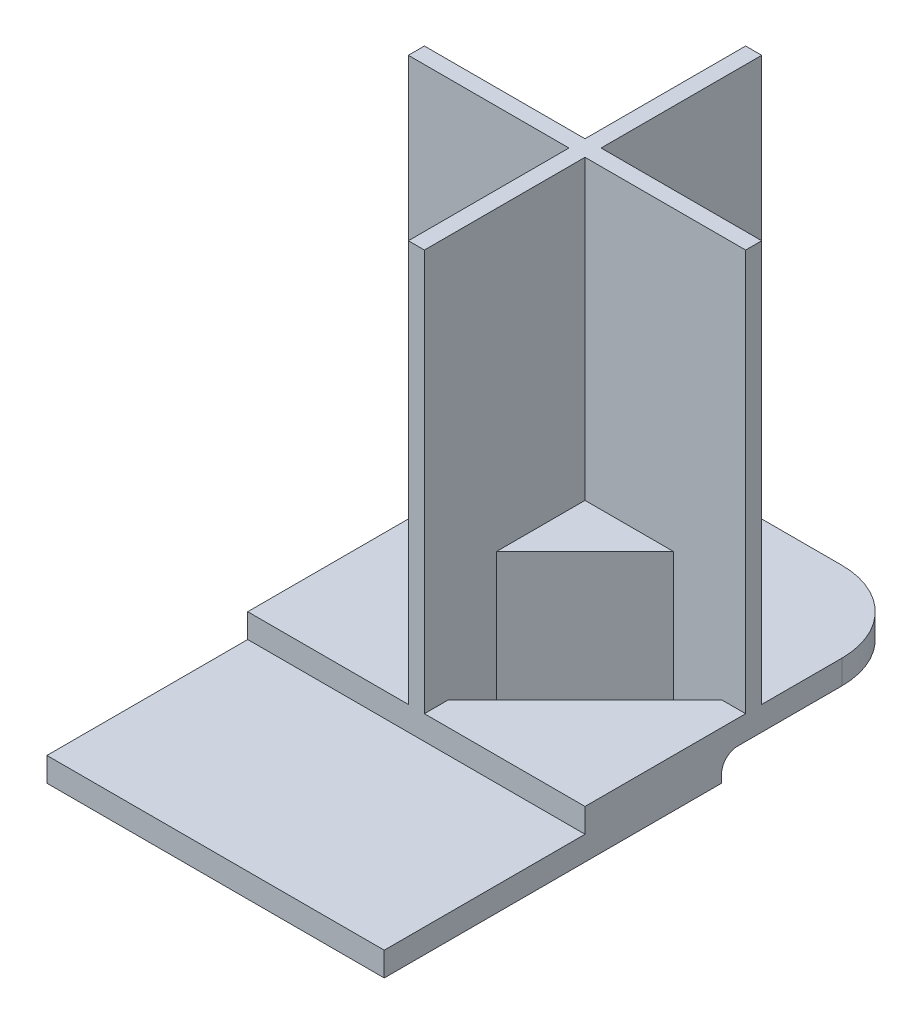
SolidWorks part; units mm, degrees
ref_plane "Front Plane" through (0, 0, 0) normal (0, 0, 1) x (1, 0, 0)
ref_plane "Top Plane" through (0, 0, 0) normal (0, 1, 0) x (1, 0, 0)
ref_plane "Right Plane" through (0, 0, 0) normal (1, 0, 0) x (0, 0, -1)
sketch "Sketch1" plane through (0, 0, 0) normal (0, 1, 0) x (1, 0, 0)
  line L1 (-21, 12.5) -> (21, 12.5)
  line L2 (-21, 12.5) -> (-21, -12.5)
  line L3 (-21, -12.5) -> (21, -12.5)
  line L4 (21, 12.5) -> (21, -12.5)
  line L5 (-21, 12.5) -> (21, -12.5) construction
  line L6 (-21, -12.5) -> (21, 12.5) construction
  point P0 (0, 0)
  dimension "D1" = 42
  dimension "D2" = 25
extrude "Boss-Extrude1" add sketch "Sketch1" along normal blind 3
sketch "Sketch2" plane through (0, 0, 0) normal (0, 1, 0) x (1, 0, 0)
  line L0 (21, -12.5) -> (21, 12.5) construction
  line L1 (-21, 12.5) -> (21, 12.5)
  line L2 (-21, 12.5) -> (-21, 29.5)
  line L3 (-21, 29.5) -> (21, 29.5)
  line L4 (21, 12.5) -> (21, 29.5)
  dimension "D2" = 17
extrude "Boss-Extrude2" add sketch "Sketch2" along normal blind 6
sketch "Sketch4" plane through (0, 0, -29.5) normal (0, 0, -1) x (-1, 0, 0)
  line L1 (-21, 6) -> (21, 6)
  line L2 (-21, 6) -> (-21, 3)
  line L3 (-21, 3) -> (21, 3)
  line L4 (21, 6) -> (21, 3)
extrude "Boss-Extrude4" add sketch "Sketch4" along normal blind 3
fillet "Fillet2" radius 2 1 edges at (0, 3, -29.5)
sketch "Sketch5" plane through (0, 0, -32.5) normal (0, 0, -1) x (-1, 0, 0)
  line L1 (-21, 6) -> (21, 6)
  line L2 (-21, 6) -> (-21, 3)
  line L3 (-21, 3) -> (21, 3)
  line L4 (21, 6) -> (21, 3)
extrude "Boss-Extrude5" add sketch "Sketch5" along normal blind 2
sketch "Sketch6" plane through (0, 6, 0) normal (0, 1, 0) x (1, 0, 0)
  line L0 (21, 12.5) -> (21, 34.5) construction
  line L1 (-21, 34.5) -> (-1, 34.5)
  line L2 (-21, 34.5) -> (-21, 32.5)
  line L3 (-21, 32.5) -> (-1, 32.5)
  line L4 (21, 34.5) -> (21, 32.5)
  line L5 (21, 12.5) -> (-21, 12.5) construction
  line L6 (-1, 12.5) -> (1, 12.5)
  line L7 (-1, 12.5) -> (-1, 32.5)
  line L8 (-1, 54.5) -> (1, 54.5)
  line L9 (1, 12.5) -> (1, 32.5)
  line L10 (1, 34.5) -> (1, 54.5)
  line L11 (1, 34.5) -> (21, 34.5)
  line L12 (-1, 34.5) -> (-1, 54.5)
  line L13 (1, 32.5) -> (21, 32.5)
  point P13 (0, 12.5)
  dimension "D1" = 2
  dimension "D2" = 42
  dimension "D3" = 2
sketch "Sketch7" plane through (0, 0, -34.5) normal (0, 0, -1) x (-1, 0, 0)
  line L1 (-21, 6) -> (21, 6)
  line L2 (-21, 6) -> (-21, 3)
  line L3 (-21, 3) -> (21, 3)
  line L4 (21, 6) -> (21, 3)
extrude "Boss-Extrude6" add sketch "Sketch7" along normal blind 20
extrude "Boss-Extrude7" add sketch "Sketch6" along normal blind 50
sketch "Sketch9" plane through (0, 6, 0) normal (0, 1, 0) x (1, 0, 0)
  line L0 (-12, 34.5) -> (-1, 45.5)
  line L1 (-1, 34.5) -> (-21, 34.5) construction
  line L2 (-1, 54.5) -> (-1, 34.5) construction
  line L3 (-1, 45.5) -> (-1, 34.5)
  line L4 (-1, 34.5) -> (-12, 34.5)
  line L5 (1, 34.5) -> (1, 45.5)
  line L6 (1, 34.5) -> (1, 54.5) construction
  line L7 (1, 45.5) -> (12, 34.5)
  line L8 (21, 34.5) -> (1, 34.5) construction
  line L9 (12, 34.5) -> (1, 34.5)
  line L10 (12, 32.5) -> (1, 32.5)
  line L11 (1, 32.5) -> (21, 32.5) construction
  line L12 (1, 32.5) -> (1, 21.5)
  line L13 (1, 12.5) -> (1, 32.5) construction
  line L14 (1, 21.5) -> (12, 32.5)
  line L15 (-1, 21.5) -> (-1, 32.5)
  line L16 (-1, 32.5) -> (-1, 12.5) construction
  line L17 (-1, 32.5) -> (-12, 32.5)
  line L18 (-21, 32.5) -> (-1, 32.5) construction
  line L19 (-12, 32.5) -> (-1, 21.5)
  dimension "D1" = 11
  dimension "D2" = 11
extrude "Boss-Extrude8" add sketch "Sketch9" along normal blind 13
sketch "Sketch10" plane through (0, 6, 0) normal (0, 1, 0) x (1, 0, 0)
  line L0 (1, 45.5) -> (1, 51.5811)
  line L1 (1, 34.5) -> (1, 54.5) construction
  line L2 (1, 51.5811) -> (18.0811, 34.5)
  line L3 (21, 34.5) -> (12, 34.5) construction
  line L4 (18.0811, 34.5) -> (12, 34.5)
  line L5 (12, 34.5) -> (1, 45.5)
  line L6 (-1, 45.5) -> (-1, 51.5811)
  line L7 (-1, 54.5) -> (-1, 45.5) construction
  line L8 (-1, 51.5811) -> (-18.0811, 34.5)
  line L9 (-12, 34.5) -> (-21, 34.5) construction
  line L10 (-18.0811, 34.5) -> (-12, 34.5)
  line L11 (-12, 34.5) -> (-1, 45.5)
  line L12 (-12, 32.5) -> (-1, 21.5)
  line L13 (-1, 21.5) -> (-1, 15.4189)
  line L14 (-1, 21.5) -> (-1, 12.5) construction
  line L15 (-1, 15.4189) -> (-18.0811, 32.5)
  line L16 (-21, 32.5) -> (-1, 32.5) construction
  line L17 (-18.0811, 32.5) -> (-12, 32.5)
  line L18 (1, 21.5) -> (1, 15.4189)
  line L19 (1, 12.5) -> (1, 21.5) construction
  line L20 (1, 15.4189) -> (18.0811, 32.5)
  line L21 (12, 32.5) -> (21, 32.5) construction
  line L22 (18.0811, 32.5) -> (12, 32.5)
  line L23 (12, 32.5) -> (1, 21.5)
  dimension "D1" = 4.3
  dimension "D2" = 4.3
  dimension "D3" = 4.3
  dimension "D4" = 4.3
extrude "Cut-Extrude1" cut sketch "Sketch10" against normal blind 13
fillet "Fillet3" radius 10 2 edges at (-21, 4.5, -54.5) (21, 4.5, -54.5)
